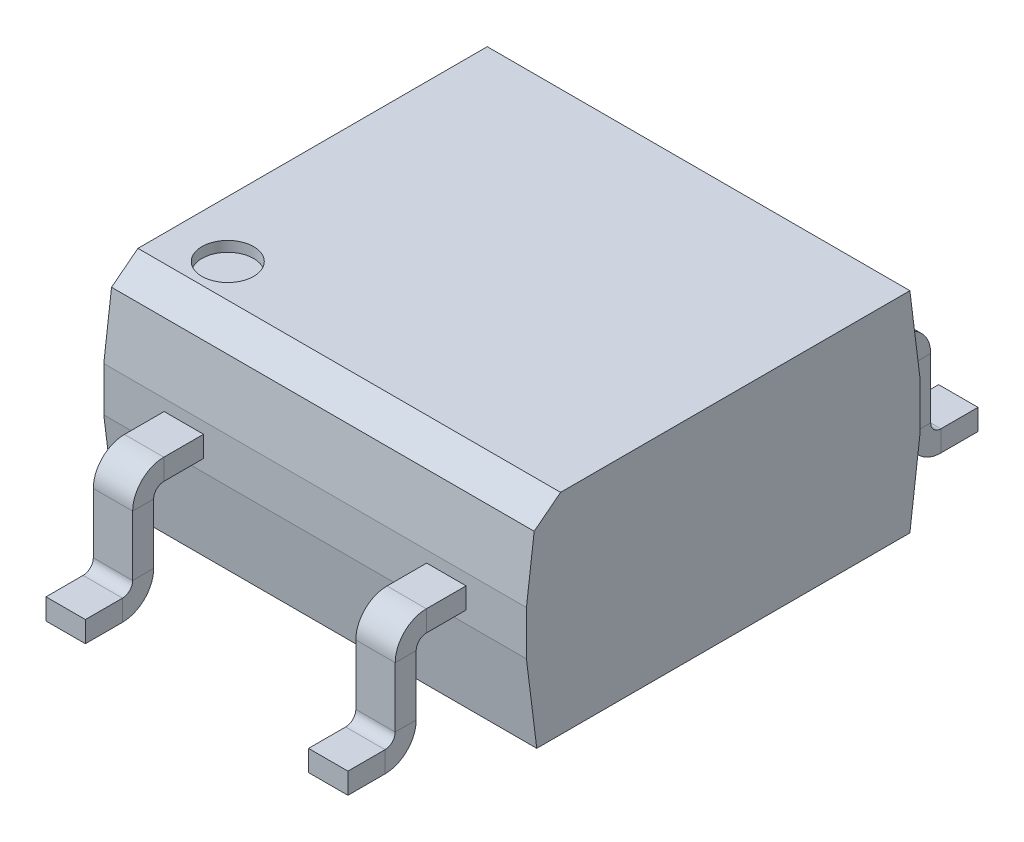
SolidWorks part; units mm, degrees
ref_plane "Спереди" through (0, 0, 0) normal (0, 0, 1) x (1, 0, 0)
ref_plane "Сверху" through (0, 0, 0) normal (0, 1, 0) x (1, 0, 0)
ref_plane "Справа" through (0, 0, 0) normal (1, 0, 0) x (0, 0, -1)
ref_plane "Плоскость1" through (0, 0.064, 0) normal (0, 1, 0) x (1, 0, 0)
sketch "Эскиз1" plane through (0, 0.064, 0) normal (0, 1, 0) x (1, 0, 0)
  line L1 (-2.0445, 1.905) -> (2.0445, 1.905)
  line L2 (-2.0445, 1.905) -> (-2.0445, -1.905)
  line L3 (-2.0445, -1.905) -> (2.0445, -1.905)
  line L4 (2.0445, 1.905) -> (2.0445, -1.905)
  line L5 (-2.0445, 1.905) -> (2.0445, -1.905) construction
  line L6 (-2.0445, -1.905) -> (2.0445, 1.905) construction
  point P0 (0, 0)
  dimension "D1" = 4.089
  dimension "D2" = 3.81
extrude "Бобышка-Вытянуть1" add sketch "Эскиз1" along normal blind 2.03
chamfer "Фаска1" distance 0.8 distance2 0.1 2 edges at (0, 2.094, -1.905) (0, 2.094, 1.905)
chamfer "Фаска2" distance 0.1 distance2 0.8 2 edges at (0, 0.064, -1.905) (0, 0.064, 1.905)
chamfer "Фаска3" distance 0.2 angle 45 1 edges at (0, 2.094, 1.805)
sketch "Эскиз2" plane through (0, 2.094, 0) normal (0, 1, 0) x (1, 0, 0)
  circle A0 centre (-1.5, -1.25) radius 0.25
extrude "Вырез-Вытянуть1" cut sketch "Эскиз2" against normal blind 0.1
sketch "Эскиз3" plane through (0, 0, 1.905) normal (0, 0, 1) x (1, 0, 0)
  line L0 (0, 0) -> (0, 2.442) construction
  line L1 (-1.4605, 1.184) -> (-1.0795, 1.184)
  line L2 (-1.4605, 1.184) -> (-1.4605, 0.981)
  line L3 (-1.4605, 0.981) -> (-1.0795, 0.981)
  line L4 (-1.0795, 1.184) -> (-1.0795, 0.981)
  line L5 (-1.4605, 1.184) -> (-1.0795, 0.981) construction
  line L6 (-1.4605, 0.981) -> (-1.0795, 1.184) construction
  line L7 (1.4605, 0.981) -> (1.0795, 0.981)
  line L8 (1.0795, 1.184) -> (1.0795, 0.981)
  line L9 (1.4605, 1.184) -> (1.0795, 1.184)
  line L10 (1.4605, 1.184) -> (1.4605, 0.981)
  point P0 (-1.27, 1.0825)
  point P5 (-1.27, 1.184)
  dimension "D1" = 0.381
  dimension "D2" = 0.203
  dimension "D3" = 1.184
  dimension "D4" = 1.27
sketch "Эскиз5" plane through (0, 0, 0) normal (1, 0, 0) x (0, 0, -1)
  line L0 (-1.905, 1.0825) -> (-2.289, 1.0825)
  line L1 (-2.489, 0.8825) -> (-2.489, 0.3015)
  line L2 (-2.689, 0.1015) -> (-3.048, 0.1015)
  arc A0 (-2.489, 0.3015) -> (-2.689, 0.1015) centre (-2.689, 0.3015) cw
  arc A1 (-2.289, 1.0825) -> (-2.489, 0.8825) centre (-2.289, 0.8825) ccw
  point P9 (-2.489, 0.592)
  dimension "D1" = 0.2
  dimension "D2" = 0.584
  dimension "D3" = 0.559
  dimension "D4" = 0.981
sweep "По траектории1" add profiles "Эскиз3" path "Эскиз5"
mirror "Зеркальное отражение1" about plane through (0, 0, 0) normal (0, 0, 1) of "По траектории1"
